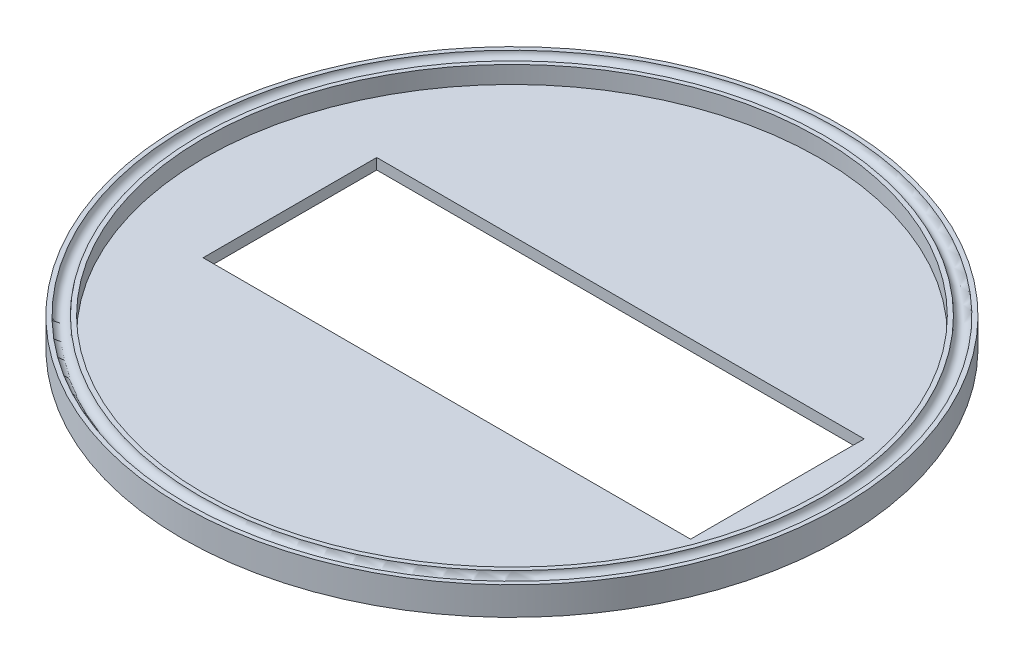
SolidWorks part; units mm, degrees
ref_plane "Front Plane" through (0, 0, 0) normal (0, 0, 1) x (1, 0, 0)
ref_plane "Top Plane" through (0, 0, 0) normal (0, 1, 0) x (1, 0, 0)
ref_plane "Right Plane" through (0, 0, 0) normal (1, 0, 0) x (0, 0, -1)
sketch "Sketch1" plane through (0, 0, 0) normal (0, 1, 0) x (1, 0, 0)
  circle A0 centre (0, 0) radius 75.925
  dimension "D1" = 151.85
extrude "Boss-Extrude1" add sketch "Sketch1" along normal blind 2.5
sketch "Sketch2" plane through (0, 2.5, 0) normal (0, 1, 0) x (1, 0, 0)
  line L0 (0, 0) -> (50000, 0) construction
  line L1 (61.15, -20) -> (-51.15, -20)
  line L2 (61.15, -20) -> (61.15, 20)
  line L3 (61.15, 20) -> (-51.15, 20)
  line L4 (-51.15, -20) -> (-51.15, 20)
  point P7 (76.15, 0)
  point P9 (-76.15, 0)
  dimension "D2" = 40
  dimension "D3" = 15
  dimension "D4" = 25
extrude "Cut-Extrude1" cut sketch "Sketch2" against normal through all
sketch "Sketch10" plane through (0, 2.5, 0) normal (0, 1, 0) x (1, 0, 0)
  circle A0 centre (0, 0) radius 75.925
  circle A1 centre (0, 0) radius 70.925
  circle A2 centre (0, 0) radius 75.925 construction
  dimension "D1" = 5
extrude "Boss-Extrude2" add sketch "Sketch10" along normal blind 4
sketch "Sketch12" plane through (0, 6.5, 0) normal (0, 1, 0) x (1, 0, 0)
  line L0 (0, 0) -> (-50000, 0) construction
  circle A0 centre (0, 0) radius 73.425
  circle A1 centre (0, 0) radius 70.925 construction
  circle A2 centre (0, 0) radius 70.925 construction
  point P3 (-70.8965, 2.011)
  point P4 (-73.425, 0)
  point P7 (-70.925, 0)
  point P8 (-70.925, 0)
  dimension "D1" = 2.5
sweep "Cut-Sweep3" cut path "Sketch12" circular profile diameter 3 parameters "D3"=3
